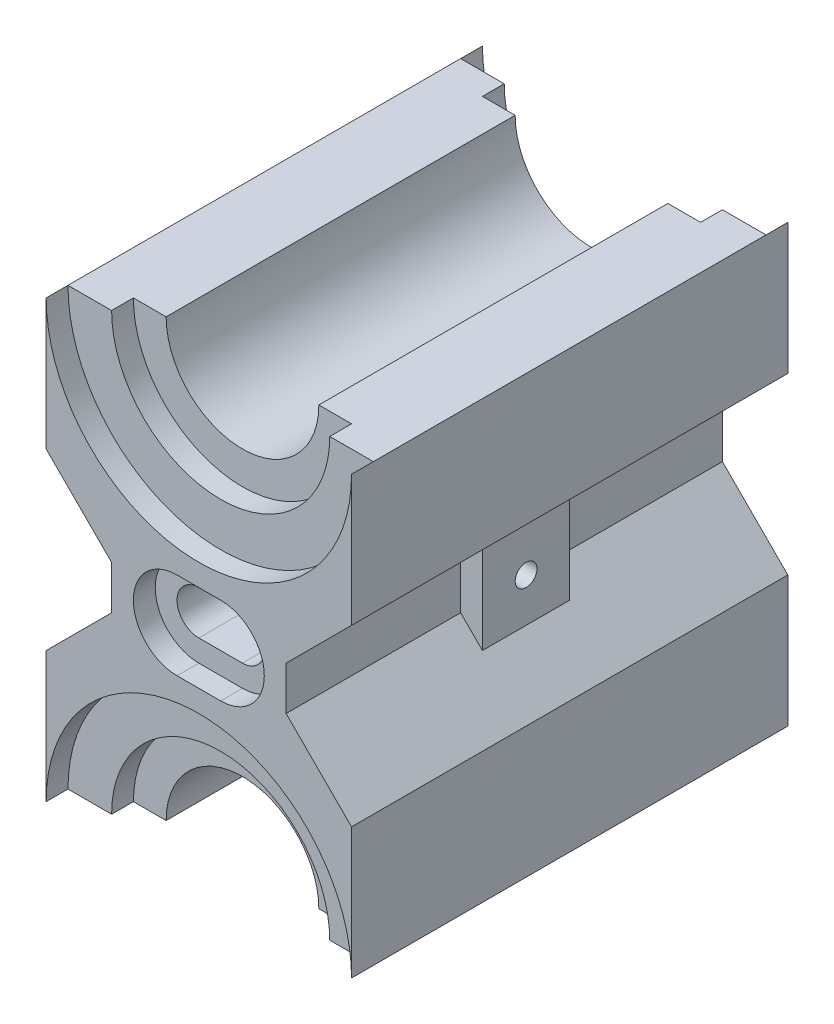
SolidWorks part; units mm, degrees
ref_plane "Front Plane" through (0, 0, 0) normal (0, 0, 1) x (1, 0, 0)
ref_plane "Top Plane" through (0, 0, 0) normal (0, 1, 0) x (1, 0, 0)
ref_plane "Right Plane" through (0, 0, 0) normal (1, 0, 0) x (0, 0, -1)
sketch "Sketch1" plane through (0, 0, 0) normal (0, 0, 1) x (1, 0, 0)
  line L0 (-70, 0) -> (-70, 30)
  line L1 (-70, 30) -> (-55, 45)
  line L2 (-55, 45) -> (-55, 55)
  line L3 (-55, 55) -> (-70, 70)
  line L4 (-70, 70) -> (-70, 100)
  line L7 (0, 70) -> (-15, 55)
  line L8 (-15, 55) -> (-15, 45)
  line L9 (-15, 45) -> (0, 30)
  line L10 (0, 30) -> (0, 0)
  line L12 (0, 70) -> (0, 100)
  arc A0 (-70, 0) -> (0, 0) centre (-35, 0) cw
  arc A1 (-70, 100) -> (0, 100) centre (-35, 100) ccw
  dimension "D1" = 15
  dimension "D2" = 15
  dimension "D5" = 15
  dimension "D6" = 10
  dimension "D7" = 15
  dimension "D8" = 15
  dimension "D9" = 15
  dimension "D10" = 15
  dimension "D11" = 30
  dimension "D14" = 30
  dimension "D15" = 30
  dimension "D16" = 40
extrude "Boss-Extrude1" add sketch "Sketch1" along normal blind 100
sketch "Sketch2" plane through (0, 0, 0) normal (0, 0, -1) x (-1, 0, 0)
  line L0 (0, 100) -> (10, 100)
  line L1 (60, 100) -> (70, 100)
  line L2 (0, 0) -> (10, 0)
  line L3 (60, 0) -> (70, 0)
  line L4 (0, 0) -> (0, 30) construction
  line L5 (70, 30) -> (70, 0) construction
  arc A0 (10, 100) -> (60, 100) centre (35, 100) ccw
  arc A1 (0, 100) -> (70, 100) centre (35, 100) ccw construction
  arc A2 (0, 100) -> (70, 100) centre (35, 100) ccw
  arc A3 (0, 0) -> (70, 0) centre (35, 0) cw
  arc A4 (10, 0) -> (60, 0) centre (35, 0) cw
  dimension "D1" = 10
  dimension "D3" = 25
  dimension "D4" = 35
  dimension "D5" = 35
  dimension "D6" = 10
  dimension "D8" = 25
  dimension "D2" = 10
  dimension "D7" = 10
extrude "Boss-Extrude2" add sketch "Sketch2" against normal blind 95
sketch "Sketch3" plane through (0, 0, 0) normal (0, 0, -1) x (-1, 0, 0)
  line L0 (0, 100) -> (10, 100)
  line L1 (60, 100) -> (70, 100)
  line L2 (60, 0) -> (70, 0)
  line L3 (0, 0) -> (10, 0)
  arc A0 (0, 100) -> (70, 100) centre (35, 100) ccw
  arc A1 (10, 100) -> (60, 100) centre (35, 100) ccw
  arc A2 (10, 100) -> (60, 100) centre (35, 100) ccw construction
  arc A3 (10, 0) -> (60, 0) centre (35, 0) cw
  arc A4 (0, 0) -> (70, 0) centre (35, 0) cw
  dimension "D1" = 25
  dimension "D2" = 35
  dimension "D3" = 25
  dimension "D4" = 35
extrude "Cut-Extrude1" cut sketch "Sketch3" against normal blind 5
sketch "Sketch4" plane through (0, 0, 5) normal (0, 0, -1) x (-1, 0, 0)
  line L0 (10, 100) -> (17.5, 100)
  line L1 (52.5, 100) -> (60, 100)
  line L2 (10, 0) -> (17.5, 0)
  line L3 (60, 0) -> (52.5, 0)
  arc A0 (17.5, 100) -> (52.5, 100) centre (35, 100) ccw
  arc A1 (10, 100) -> (60, 100) centre (35, 100) ccw
  arc A2 (60, 0) -> (10, 0) centre (35, 0) ccw construction
  arc A3 (10, 0) -> (60, 0) centre (35, 0) cw
  arc A4 (17.5, 0) -> (52.5, 0) centre (35, 0) cw
  dimension "D1" = 7.5
  dimension "D3" = 17.5
  dimension "D4" = 25
  dimension "D5" = 7.5
  dimension "D7" = 17.5
  dimension "D2" = 7.5
  dimension "D6" = 7.5
extrude "Boss-Extrude5" add sketch "Sketch4" against normal blind 85
sketch "Sketch7" plane through (0, 0, 5) normal (0, 0, -1) x (-1, 0, 0)
  line L0 (17.5, 100) -> (10, 100)
  line L1 (17.5, 100) -> (0, 100) construction
  line L2 (70, 100) -> (52.5, 100) construction
  line L3 (0, 0) -> (17.5, 0) construction
  line L4 (52.5, 0) -> (70, 0) construction
  line L5 (10, 0) -> (17.5, 0)
  line L6 (52.5, 0) -> (60, 0)
  arc A0 (10, 100) -> (60, 100) centre (35, 100) ccw
  arc A1 (17.5, 100) -> (52.5, 100) centre (35, 100) ccw
  arc A2 (10, 0) -> (60, 0) centre (35, 0) cw
  arc A3 (17.5, 0) -> (52.5, 0) centre (35, 0) cw
  line M2 (70, 100) -> (52.5, 100)
  arc M3 (52.5, 100) -> (17.5, 100) centre (35, 100) cw
  line M4 (17.5, 100) -> (0, 100)
  dimension "D1" = 7.5
  dimension "D3" = 17.5
  dimension "D4" = 25
  dimension "D5" = 7.5
  dimension "D7" = 17.5
  dimension "D8" = 25
  dimension "D2" = 7.5
  dimension "D6" = 7.5
extrude "Cut-Extrude4" cut sketch "Sketch7" against normal blind 5 contours A0 M4 M2 M3 | L5 A3 L6 A2
sketch "Sketch9" plane through (0, 0, 0) normal (0, 0, -1) x (-1, 0, 0)
  line L0 (10, 40) -> (15, 45)
  line L1 (0, 30) -> (15, 45) construction
  line L2 (15, 45) -> (15, 55)
  line L3 (15, 55) -> (10, 60)
  line L4 (15, 55) -> (0, 70) construction
  line L5 (10, 60) -> (10, 40)
  line L6 (60, 60) -> (55, 55)
  line L7 (70, 70) -> (55, 55) construction
  line L8 (55, 55) -> (55, 45)
  line L9 (55, 45) -> (60, 40)
  line L10 (55, 45) -> (70, 30) construction
  line L11 (60, 40) -> (60, 60)
  dimension "D1" = 5
  dimension "D2" = 5
extrude "Boss-Extrude6" add sketch "Sketch9" against normal blind 60
sketch "Sketch10" plane through (0, 0, 0) normal (0, 0, -1) x (-1, 0, 0)
  line L0 (10, 40) -> (15, 45)
  line L1 (15, 45) -> (15, 55)
  line L2 (15, 55) -> (10, 60)
  line L3 (10, 60) -> (10, 40)
  line L5 (10, 60) -> (0, 70) construction
  line L6 (0, 30) -> (10, 40) construction
  line L7 (60, 40) -> (55, 45)
  line L8 (55, 45) -> (55, 55)
  line L9 (55, 55) -> (60, 60)
  line L10 (60, 60) -> (60, 40)
  line L11 (70, 70) -> (60, 60) construction
  dimension "D1" = 5
extrude "Cut-Extrude5" cut sketch "Sketch10" against normal blind 40
sketch "Sketch11" plane through (-10, 0, 0) normal (1, 0, 0) x (0, 0, -1)
  line L0 (-60, 60) -> (-40, 60) construction
  line L1 (-40, 60) -> (-40, 40) construction
  circle A0 centre (-50, 50) radius 2.5
  dimension "D1" = 5
  dimension "D3" = 10
  dimension "D2" = 10
extrude "Cut-Extrude6" cut sketch "Sketch11" against normal blind 15
sketch "Sketch12" plane through (-60, 0, 0) normal (-1, 0, 0) x (0, 0, 1)
  line L1 (60, 60) -> (40, 60) construction
  line L2 (60, 40) -> (60, 60) construction
  circle A0 centre (50, 50) radius 2.5
  dimension "D1" = 5
  dimension "D2" = 10
  dimension "D3" = 10
extrude "Cut-Extrude7" cut sketch "Sketch12" against normal blind 15
sketch "Sketch13" plane through (0, 0, 0) normal (0, 0, -1) x (-1, 0, 0)
  line L0 (30, 50) -> (40, 50) construction
  line L1 (30, 60) -> (40, 60)
  line L2 (30, 40) -> (40, 40)
  line L3 (10, 60) -> (10, 40) construction
  arc A0 (30, 60) -> (30, 40) centre (30, 50) ccw
  arc A1 (40, 40) -> (40, 60) centre (40, 50) ccw
  point P2 (35, 50)
  dimension "D1" = 10
  dimension "D2" = 20
extrude "Cut-Extrude8" cut sketch "Sketch13" against normal blind 5
sketch "Sketch14" plane through (0, 0, 5) normal (0, 0, -1) x (-1, 0, 0)
  line L0 (30, 50) -> (40, 50) construction
  line L1 (30, 55) -> (40, 55)
  line L2 (30, 45) -> (40, 45)
  line L3 (40, 60) -> (30, 60) construction
  line L4 (30, 40) -> (40, 40) construction
  arc A0 (30, 55) -> (30, 45) centre (30, 50) ccw
  arc A1 (40, 45) -> (40, 55) centre (40, 50) ccw
  point P2 (35, 50)
  dimension "D1" = 10
  dimension "D2" = 5
  dimension "D3" = 5
extrude "Cut-Extrude9" cut sketch "Sketch14" against normal blind 30
sketch "Sketch15" plane through (0, 0, 100) normal (0, 0, 1) x (1, 0, 0)
  line L0 (-40, 50) -> (-30, 50) construction
  line L1 (-40, 60) -> (-30, 60)
  line L2 (-40, 40) -> (-30, 40)
  line L3 (-55, 55) -> (-55, 45) construction
  arc A0 (-40, 60) -> (-40, 40) centre (-40, 50) ccw
  arc A1 (-30, 40) -> (-30, 60) centre (-30, 50) ccw
  point P2 (-35, 50)
  dimension "D1" = 10
  dimension "D2" = 15
extrude "Cut-Extrude10" cut sketch "Sketch15" against normal blind 5
sketch "Sketch16" plane through (0, 0, 95) normal (0, 0, 1) x (1, 0, 0)
  line L0 (-40, 50) -> (-30, 50) construction
  line L1 (-40, 55) -> (-30, 55)
  line L2 (-40, 45) -> (-30, 45)
  line L3 (-30, 60) -> (-40, 60) construction
  line L4 (-40, 40) -> (-30, 40) construction
  arc A0 (-40, 55) -> (-40, 45) centre (-40, 50) ccw
  arc A1 (-30, 45) -> (-30, 55) centre (-30, 50) ccw
  point P2 (-35, 50)
  dimension "D1" = 5
  dimension "D2" = 5
extrude "Cut-Extrude11" cut sketch "Sketch16" against normal blind 30
